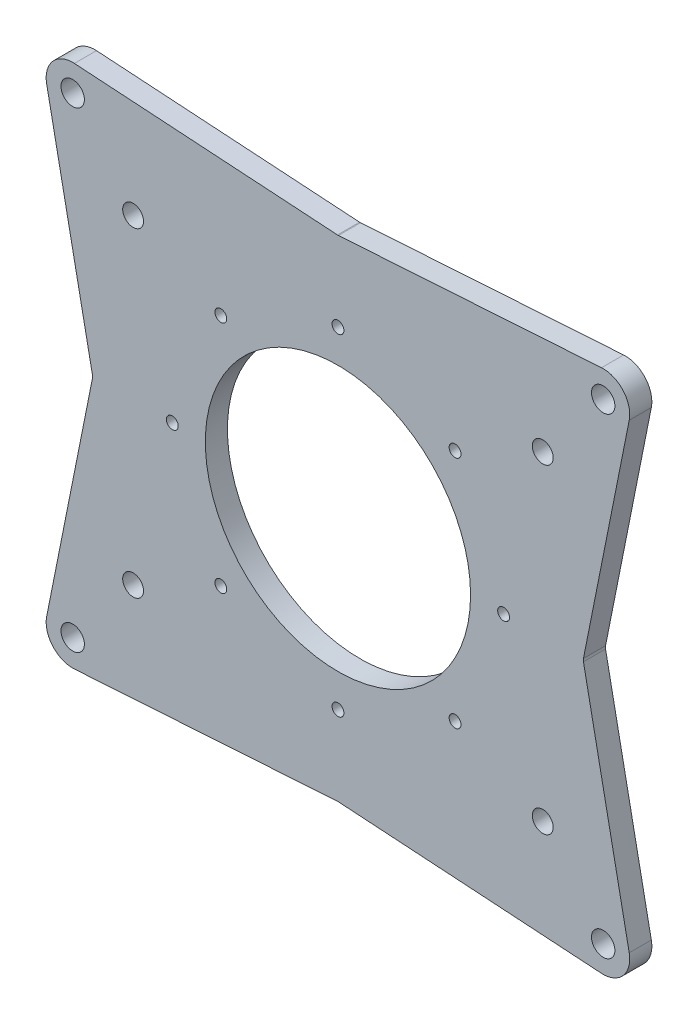
SolidWorks part; units mm, degrees
material "6061 Alloy"
ref_plane "Front Plane" through (0, 0, 0) normal (0, 0, 1) x (1, 0, 0)
ref_plane "Top Plane" through (0, 0, 0) normal (0, 1, 0) x (1, 0, 0)
ref_plane "Right Plane" through (0, 0, 0) normal (1, 0, 0) x (0, 0, -1)
sketch "Base Sketch" plane through (0, 0, 0) normal (0, 0, 1) x (1, 0, 0)
  line L0 (-125.5086, 99.3614) -> (-105.664, 0)
  line L1 (-88.2572, -68.9541) -> (88.2572, -68.9541) construction
  line L2 (-88.2572, -68.9541) -> (-88.2572, 68.9541) construction
  line L3 (-88.2572, 68.9541) -> (88.2572, 68.9541) construction
  line L4 (88.2572, -68.9541) -> (88.2572, 68.9541) construction
  line L5 (-88.2572, -68.9541) -> (88.2572, 68.9541) construction
  line L6 (-88.2572, 68.9541) -> (88.2572, -68.9541) construction
  line L7 (-114.3, 101.6) -> (114.3, 101.6) construction
  line L8 (-114.3, 101.6) -> (-114.3, -101.6) construction
  line L9 (-114.3, -101.6) -> (114.3, -101.6) construction
  line L10 (114.3, 101.6) -> (114.3, -101.6) construction
  line L11 (-114.3, 101.6) -> (114.3, -101.6) construction
  line L12 (-114.3, -101.6) -> (114.3, 101.6) construction
  line L15 (105.664, 0) -> (125.5086, 99.3614)
  line L16 (105.664, 0) -> (125.5086, -99.3614)
  line L19 (-125.5086, -99.3614) -> (-105.664, 0)
  line L20 (-113.5626, 113.0062) -> (0, 105.664)
  line L21 (113.5626, 113.0062) -> (0, 105.664)
  line L22 (-113.5626, -113.0062) -> (0, -105.664)
  line L23 (0, -105.664) -> (113.5626, -113.0062)
  line L24 (0, 71.375) -> (0, 0) construction
  circle A1 centre (0, 0) radius 57.15
  arc A2 (-125.5086, 99.3614) -> (-113.5626, 113.0062) centre (-114.3, 101.6) cw
  arc A3 (113.5626, 113.0062) -> (125.5086, 99.3614) centre (114.3, 101.6) cw
  arc A4 (113.5626, -113.0062) -> (125.5086, -99.3614) centre (114.3, -101.6) ccw
  arc A5 (-113.5626, -113.0062) -> (-125.5086, -99.3614) centre (-114.3, -101.6) cw
  circle A9 centre (0, 0) radius 105.664 construction
  point P1 (50.4697, 50.4697)
  point P16 (0, 71.375)
  point P25 (71.375, 0)
  point P26 (50.4697, -50.4697)
  point P27 (0, -71.375)
  point P28 (-50.4697, -50.4697)
  point P29 (-71.375, 0)
  point P30 (-50.4697, 50.4697)
  point P32 (0, 0)
  dimension "D3" = 211.328
  dimension "D4" = 114.3
  dimension "D7" = 11.43
  dimension "D1" = 137.9082
  dimension "D2" = 176.5144
  dimension "D5" = 203.2
  dimension "D6" = 228.6
  dimension "D8" = 8
  dimension "D9" = 71.375
extrude "Boss-Extrude1" add sketch "Base Sketch" along normal blind 9.525
hole_wizard "Chassis Mounting 3/8 Clearance Hole" positions "Sketch6" profile "Sketch5" hole size "3/8" standard "ANSI Inch" end condition through all
sketch "Sketch6" plane through (0, 0, 0) normal (0, 0, -1) x (-1, 0, 0)
  point P0 (-114.3, 101.6)
  point P3 (-114.3, -101.6)
  point P6 (114.3, -101.6)
  point P9 (114.3, 101.6)
sketch "Sketch5" plane through (114.3, 101.6, 0) normal (1, 0, 0) x (0, 1, 0)
  line L0 (0, 0) -> (0, 9.525)
  line L1 (0, 9.525) -> (5.0419, 9.525)
  line L2 (5.0419, 9.525) -> (5.0419, 0)
  line L5 (5.0419, 0) -> (0, 0)
  line L11 (0, -6.35) -> (0, 107.95) construction
  dimension "Thru Hole Dia." = 10.0838
  dimension "Thru Hole Depth" = 9.525
hole_wizard "Motor Mounting M8 Clearance Hole" positions "Sketch8" profile "Sketch7" hole size "M8" standard "ISO" end condition through all
sketch "Sketch8" plane through (0, 0, 0) normal (0, 0, -1) x (-1, 0, 0)
  point P0 (-88.2572, 68.9541)
  point P3 (88.2572, 68.9541)
  point P6 (88.2572, -68.9541)
  point P9 (-88.2572, -68.9541)
sketch "Sketch7" plane through (88.2572, 68.9541, 0) normal (1, 0, 0) x (0, 1, 0)
  line L0 (0, 0) -> (0, 9.525)
  line L1 (0, 9.525) -> (4.5, 9.525)
  line L2 (4.5, 9.525) -> (4.5, 0)
  line L5 (4.5, 0) -> (0, 0)
  line L11 (0, -6.35) -> (0, 107.95) construction
  dimension "Thru Hole Dia." = 9
  dimension "Thru Hole Depth" = 9.525
hole_wizard "Ring Gear 1/4-20 Tapped Hole" positions "Sketch11" profile "Sketch12" tap size "1/4-20" standard "ANSI Inch" end condition through all
sketch "Sketch11" plane through (0, 0, 0) normal (0, 0, -1) x (-1, 0, 0)
  point P0 (-50.4697, 50.4697)
  point P3 (-71.375, 0)
  point P6 (-50.4697, -50.4697)
  point P9 (50.4697, -50.4697)
  point P12 (71.375, 0)
  point P15 (50.4697, 50.4697)
  point P18 (0, 71.375)
  point P22 (0, -71.375)
sketch "Sketch12" plane through (50.4697, 50.4697, 0) normal (1, 0, 0) x (0, 1, 0)
  line L0 (0, 0) -> (0, 9.525)
  line L1 (0, 9.525) -> (2.5527, 9.525)
  line L2 (2.5527, 9.525) -> (2.5527, 0)
  line L5 (2.5527, 0) -> (0, 0)
  line L11 (0, -6.35) -> (0, 107.95) construction
  dimension "Thru Tap Drill Dia." = 5.1054
  dimension "Thru Tap Drill Depth" = 9.525
cosmetic thread "Hole Thread1" parameters "D2"=6.35
cosmetic thread "Hole Thread2" parameters "D2"=6.35
cosmetic thread "Hole Thread3" parameters "D2"=6.35
cosmetic thread "Hole Thread4" parameters "D2"=6.35
cosmetic thread "Hole Thread5" parameters "D2"=6.35
cosmetic thread "Hole Thread6" parameters "D2"=6.35
cosmetic thread "Hole Thread7" parameters "D2"=6.35
cosmetic thread "Hole Thread8" parameters "D2"=6.35
sketch "Cut Out" plane through (0, 0, 0) normal (0, 0, -1) x (-1, 0, 0)
  line L4 (114.3, 101.6) -> (88.2572, 68.9541) construction
  line L5 (88.2572, 68.9541) -> (71.375, 0) construction
  line L7 (95.8214, 0) -> (112.0949, 81.481)
  line L11 (0, 71.375) -> (88.2572, 68.9541) construction
  line L12 (0, 71.375) -> (0, 105.664) construction
  line L13 (90.4808, 57.7425) -> (79.1717, 11.5515)
  line L14 (0, 105.664) -> (113.5626, 113.0062) construction
  line L15 (46.2641, 65.2781) -> (77.7676, 64.414)
  line L16 (125.5086, 99.3614) -> (105.664, 0) construction
  line L17 (81.1057, 60.0378) -> (73.9091, 30.6439)
  line L19 (106.4994, 84.0828) -> (98.4912, 74.0442)
  line L20 (90.946, 80.0633) -> (104.066, 96.5099)
  line L21 (102.9179, 102.6458) -> (0, 95.9918)
  line L23 (0, 55) -> (0, -55) construction
  line L24 (71.375, 0) -> (105.664, 0) construction
  line L25 (-71.375, 0) -> (-105.664, 0) construction
  line L26 (0, 71.375) -> (-88.2572, 68.9541) construction
  line L27 (-88.2572, 68.9541) -> (-71.375, 0) construction
  line L28 (-114.3, 101.6) -> (-88.2572, 68.9541) construction
  line L29 (-102.9179, 102.6458) -> (0, 95.9918)
  line L30 (-90.946, 80.0633) -> (-104.066, 96.5099)
  line L33 (-81.1057, 60.0378) -> (-73.9091, 30.6439)
  line L34 (-46.2641, 65.2781) -> (-77.7676, 64.414)
  line L35 (-90.4808, 57.7425) -> (-79.1717, 11.5515)
  line L38 (55, 0) -> (-55, 0) construction
  line L39 (-114.3, -101.6) -> (-88.2572, -68.9541) construction
  line L40 (-88.2572, -68.9541) -> (-71.375, 0) construction
  line L41 (0, -71.375) -> (-88.2572, -68.9541) construction
  line L42 (0, -71.375) -> (0, -105.664) construction
  line L43 (0, -71.375) -> (88.2572, -68.9541) construction
  line L44 (88.2572, -68.9541) -> (71.375, 0) construction
  line L45 (114.3, -101.6) -> (88.2572, -68.9541) construction
  line L47 (-90.4808, -57.7425) -> (-79.1717, -11.5515)
  line L48 (-46.2641, -65.2781) -> (-77.7676, -64.414)
  line L49 (-81.1057, -60.0378) -> (-73.9091, -30.6439)
  line L52 (-90.946, -80.0633) -> (-104.066, -96.5099)
  line L53 (-102.9179, -102.6458) -> (0, -95.9918)
  line L54 (102.9179, -102.6458) -> (0, -95.9918)
  line L55 (90.946, -80.0633) -> (104.066, -96.5099)
  line L58 (81.1057, -60.0378) -> (73.9091, -30.6439)
  line L59 (46.2641, -65.2781) -> (77.7676, -64.414)
  line L60 (90.4808, -57.7425) -> (79.1717, -11.5515)
  line L62 (26.556, 75.4744) -> (78.0322, 74.0624)
  line L63 (-26.556, 75.4744) -> (-78.0322, 74.0624)
  line L64 (26.556, -75.4744) -> (78.0322, -74.0624)
  line L65 (-26.556, -75.4744) -> (-78.0322, -74.0624)
  line L66 (-95.8214, 0) -> (-112.0949, 81.481)
  line L67 (-106.4994, 84.0828) -> (-98.4912, 74.0442)
  line L68 (95.8214, 0) -> (112.0949, -81.481)
  line L69 (106.4994, -84.0828) -> (98.4912, -74.0442)
  line L70 (-106.4994, -84.0828) -> (-98.4912, -74.0442)
  line L71 (-95.8214, 0) -> (-112.0949, -81.481)
  circle A0 centre (0, 0) radius 105.664 construction
  circle A1 centre (0, 0) radius 80.01 construction
  arc A2 (79.1717, 11.5515) -> (79.1717, -11.5515) centre (0, 0) cw
  circle A3 centre (88.2572, 68.9541) radius 11.43 construction
  circle A4 centre (114.3, 101.6) radius 11.43 construction
  arc A5 (125.5086, 99.3614) -> (113.5626, 113.0062) centre (114.3, 101.6) ccw construction
  arc A6 (90.4808, 57.7425) -> (98.4912, 74.0442) centre (88.2572, 68.9541) ccw
  arc A7 (81.1057, 60.0378) -> (77.7676, 64.414) centre (88.2572, 68.9541) cw
  arc A8 (78.0322, 74.0624) -> (90.946, 80.0633) centre (88.2572, 68.9541) cw
  arc A9 (104.066, 96.5099) -> (102.9179, 102.6458) centre (114.3, 101.6) cw
  circle A11 centre (-114.3, 101.6) radius 11.43 construction
  circle A12 centre (-88.2572, 68.9541) radius 11.43 construction
  arc A14 (-104.066, 96.5099) -> (-102.9179, 102.6458) centre (-114.3, 101.6) ccw
  arc A15 (-78.0322, 74.0624) -> (-90.946, 80.0633) centre (-88.2572, 68.9541) ccw
  arc A16 (-81.1057, 60.0378) -> (-77.7676, 64.414) centre (-88.2572, 68.9541) ccw
  arc A17 (-90.4808, 57.7425) -> (-98.4912, 74.0442) centre (-88.2572, 68.9541) cw
  arc A18 (-79.1717, 11.5515) -> (-79.1717, -11.5515) centre (0, 0) ccw
  circle A19 centre (-88.2572, -68.9541) radius 11.43 construction
  circle A20 centre (-114.3, -101.6) radius 11.43 construction
  circle A21 centre (114.3, -101.6) radius 11.43 construction
  circle A22 centre (88.2572, -68.9541) radius 11.43 construction
  arc A23 (-90.4808, -57.7425) -> (-98.4912, -74.0442) centre (-88.2572, -68.9541) ccw
  arc A24 (-81.1057, -60.0378) -> (-77.7676, -64.414) centre (-88.2572, -68.9541) cw
  arc A25 (-78.0322, -74.0624) -> (-90.946, -80.0633) centre (-88.2572, -68.9541) cw
  arc A26 (-104.066, -96.5099) -> (-102.9179, -102.6458) centre (-114.3, -101.6) cw
  arc A29 (104.066, -96.5099) -> (102.9179, -102.6458) centre (114.3, -101.6) ccw
  arc A30 (78.0322, -74.0624) -> (90.946, -80.0633) centre (88.2572, -68.9541) ccw
  arc A31 (81.1057, -60.0378) -> (77.7676, -64.414) centre (88.2572, -68.9541) ccw
  arc A32 (90.4808, -57.7425) -> (98.4912, -74.0442) centre (88.2572, -68.9541) cw
  arc A33 (46.2641, 65.2781) -> (73.9091, 30.6439) centre (0, 0) cw
  arc A37 (-46.2641, 65.2781) -> (-73.9091, 30.6439) centre (0, 0) ccw
  arc A38 (46.2641, -65.2781) -> (73.9091, -30.6439) centre (0, 0) ccw
  arc A39 (-46.2641, -65.2781) -> (-73.9091, -30.6439) centre (0, 0) cw
  arc A40 (26.556, 75.4744) -> (-26.556, 75.4744) centre (0, 0) ccw
  arc A41 (112.0949, 81.481) -> (106.4994, 84.0828) centre (108.9814, 82.1028) ccw
  arc A42 (26.556, -75.4744) -> (-26.556, -75.4744) centre (0, 0) cw
  arc A43 (-112.0949, 81.481) -> (-106.4994, 84.0828) centre (-108.9814, 82.1028) cw
  arc A44 (112.0949, -81.481) -> (106.4994, -84.0828) centre (108.9814, -82.1028) cw
  arc A45 (-112.0949, -81.481) -> (-106.4994, -84.0828) centre (-108.9814, -82.1028) ccw
  point P0 (-88.2572, 68.9541)
  point P1 (-71.375, 0)
  point P3 (71.375, 0)
  point P5 (0, 71.375)
  point P7 (0, -71.375)
  point P9 (88.2572, 68.9541)
  point P11 (88.2572, -68.9541)
  point P13 (-88.2572, -68.9541)
  point P15 (-114.3, -101.6)
  point P17 (-114.3, 101.6)
  point P19 (114.3, 101.6)
  point P21 (114.3, -101.6)
  point P71 (114.6569, 94.3086)
  dimension "D1" = 160.02
  dimension "D6" = 22.86
  dimension "D11" = 3.175
  dimension "D2" = 4.826
  dimension "D3" = 4.826
  dimension "D4" = 4.826
  dimension "D5" = 9.652
  dimension "D7" = 4.826
  dimension "D8" = 4.826
  dimension "D9" = 9.652
  dimension "D10" = 4.826
extrude "Cut-Extrude1" cut sketch "Cut Out" against normal blind 6.35
fillet "Cut Out Fillet" radius 3.175 52 edges at (-26.556, 75.4744, 3.175) (0, 95.9918, 3.175) (-79.1717, 11.5515, 3.175) (-46.2641, 65.2781, 3.175) (-73.9091, 30.6439, 3.175) (-81.1057, 60.0378, 3.175) (-77.7676, 64.414, 3.175) (-90.4808, 57.7425, 3.175) (-98.4912, 74.0442, 3.175) (-104.066, 96.5099, 3.175) (-102.9179, 102.6458, 3.175) (-90.946, 80.0633, 3.175) (-78.0322, 74.0624, 3.175) (-79.1717, -11.5515, 3.175) (-90.4808, -57.7425, 3.175) (-46.2641, -65.2781, 3.175) (-73.9091, -30.6439, 3.175) (-81.1057, -60.0378, 3.175) (-77.7676, -64.414, 3.175) (-102.9179, -102.6458, 3.175) (-104.066, -96.5099, 3.175) (-90.946, -80.0633, 3.175) (-78.0322, -74.0624, 3.175) (0, -95.9918, 3.175) (-26.556, -75.4744, 3.175) (26.556, -75.4744, 3.175) (102.9179, -102.6458, 3.175) (104.066, -96.5099, 3.175) (90.946, -80.0633, 3.175) (78.0322, -74.0624, 3.175) (81.1057, -60.0378, 3.175) (77.7676, -64.414, 3.175) (46.2641, -65.2781, 3.175) (73.9091, -30.6439, 3.175) (90.4808, -57.7425, 3.175) (73.9091, 30.6439, 3.175) (81.1057, 60.0378, 3.175) (77.7676, 64.414, 3.175) (46.2641, 65.2781, 3.175) (79.1717, -11.5515, 3.175) (79.1717, 11.5515, 3.175) (90.4808, 57.7425, 3.175) (104.066, 96.5099, 3.175) (102.9179, 102.6458, 3.175) (90.946, 80.0633, 3.175) (78.0322, 74.0624, 3.175) (26.556, 75.4744, 3.175) (98.4912, -74.0442, 3.175) (-98.4912, -74.0442, 3.175) (98.4912, 74.0442, 3.175) (-95.8214, 0, 3.175) (95.8214, 0, 3.175)
fillet "Outside Contour Fillet" radius 3.175 4 edges at (-105.664, 0, 4.7625) (105.664, 0, 4.7625) (0, -105.664, 4.7625) (0, 105.664, 4.7625)
ref_plane "Centerline" through (0, 0, 4.7625) normal (0, 0, -1) x (-1, 0, 0)
